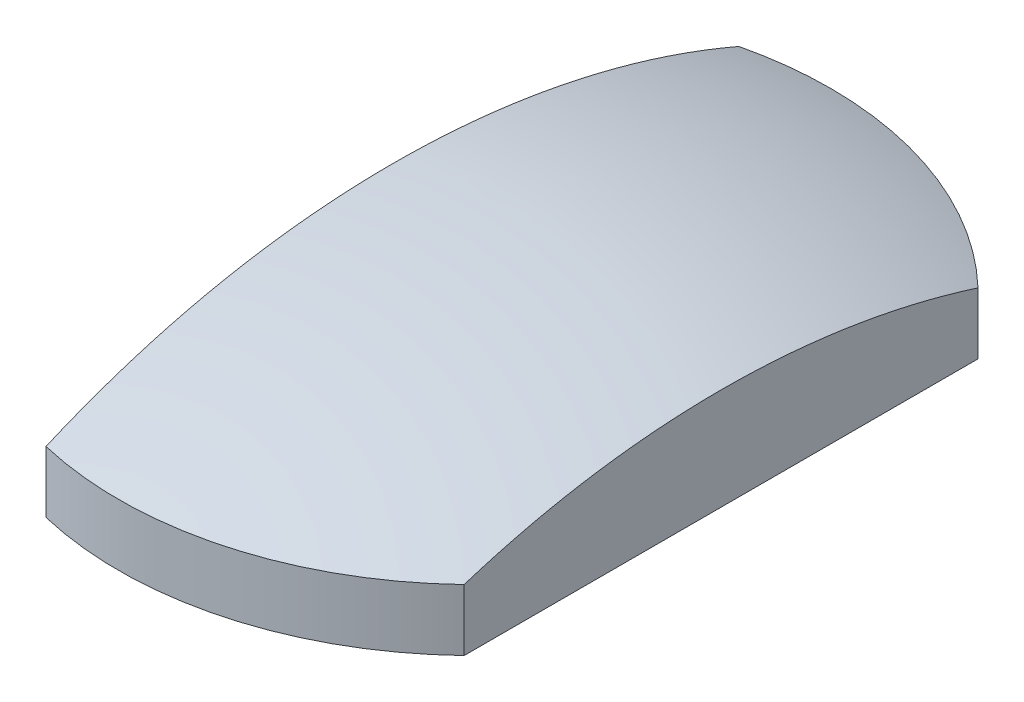
SolidWorks part; units mm, degrees
material "Стекло"
ref_plane "Спереди" through (0, 0, 0) normal (0, 0, 1) x (1, 0, 0)
ref_plane "Сверху" through (0, 0, 0) normal (0, 1, 0) x (1, 0, 0)
ref_plane "Справа" through (0, 0, 0) normal (1, 0, 0) x (0, 0, -1)
sketch "Эскиз1" plane through (0, 0, 0) normal (1, 0, 0) x (0, 0, -1)
  line L0 (0, 8) -> (15, 8) construction
  line L1 (0, 0) -> (15, 0) construction
  line L2 (13, 1.2177) -> (13, 5.246)
  line L3 (0, 8) -> (0, 0)
  arc A0 (13, 5.246) -> (0, 8) centre (0, -24.06) ccw
  arc A1 (0, 0) -> (13, 1.2177) centre (0, 70) ccw
  dimension "D1" = 32.06
  dimension "D2" = 70
  dimension "D3" = 13
  dimension "D4" = 8
revolve "Повернуть1" add sketch "Эскиз1" angle 360 about L3
ref_plane "Плоскость1" through (0, 8, 0) normal (0, 1, 0) x (-1, 0, 0)
sketch "Эскиз2" plane through (0, 8, 0) normal (0, -1, 0) x (1, 0, 0)
  line L0 (-3, 14) -> (-3, -14)
  line L1 (9, 14) -> (9, -14)
  line L2 (-3, 14) -> (9, 14)
  line L3 (-3, -14) -> (9, -14)
  dimension "D1" = 9
  dimension "D2" = 12
  dimension "D3" = 14
  dimension "D4" = 28
extrude "Вырез-Вытянуть1" cut sketch "Эскиз2" along normal through all flip side to cut contours L3 L0 L2 L1
sketch "Эскиз3" plane through (0, 0, 0) normal (1, 0, 0) x (0, 0, -1)
  line L1 (-15, 0) -> (15, 0)
  line L2 (-15, 0) -> (-15, 3)
  line L3 (-15, 3) -> (15, 3)
  line L4 (15, 0) -> (15, 3)
  dimension "D1" = 30
  dimension "D2" = 3
extrude "Вырез-Вытянуть2" cut sketch "Эскиз3" against normal through all and the other way through all
